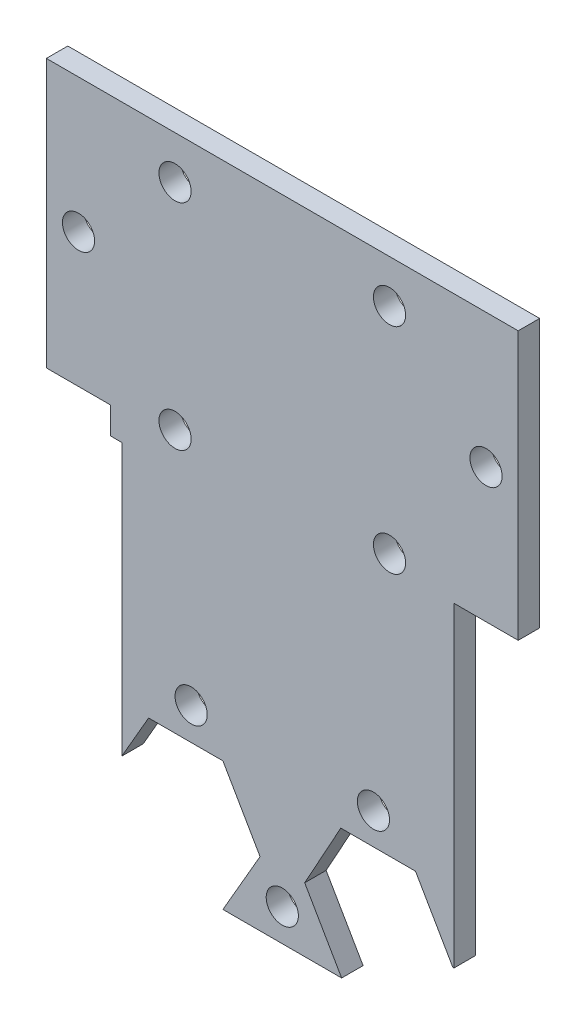
SolidWorks part; units mm, degrees
ref_plane "Front Plane" through (0, 0, 0) normal (0, 0, 1) x (1, 0, 0)
ref_plane "Top Plane" through (0, 0, 0) normal (0, 1, 0) x (1, 0, 0)
ref_plane "Right Plane" through (0, 0, 0) normal (1, 0, 0) x (0, 0, -1)
sketch "Sketch1" plane through (0, 0, 0) normal (0, 0, 1) x (1, 0, 0)
  line L0 (-15, -46.5) -> (15, -46.5) construction
  line L1 (-16, 14) -> (16, 14)
  line L2 (-16, 14) -> (-16, -13.5)
  line L3 (-16, -13.5) -> (16, -13.5)
  line L4 (16, 14) -> (16, -13.5)
  line L5 (-16, -13.5) -> (16, -13.5)
  line L6 (-16, -13.5) -> (-16, -46.5)
  line L7 (-16, -46.5) -> (16, -46.5)
  line L8 (16, -13.5) -> (16, -46.5)
  line L10 (-16, -46.5) -> (-14.9693, -46.5)
  line L11 (-16, -46.5) -> (-16, -13.5)
  line L12 (-16, -13.5) -> (-14.9693, -13.5)
  line L13 (-14.9693, -46.5) -> (-14.9693, -13.5)
  line L14 (15, -46.5) -> (15, -28.5) construction
  line L15 (16, -46.5) -> (15, -46.5)
  line L16 (16, -46.5) -> (16, -13.5)
  line L17 (16, -13.5) -> (15, -13.5)
  line L18 (15, -46.5) -> (15, -13.5)
  line L19 (16, -13.5) -> (-16, -13.5) construction
  line L20 (16, -13) -> (16, -6.5) construction
  line L21 (-16, 13.5) -> (16, 13.5) construction
  line L22 (-16, 14) -> (16, 14) construction
  line L23 (-16, 14) -> (-16, 39)
  line L24 (-16, 39) -> (16, 39)
  line L25 (16, 14) -> (16, 39)
  line L26 (9.5, 20.5152) -> (0, 15.0303)
  line L27 (0, 15.0303) -> (-9.5, 20.5152)
  line L28 (-9.5, 20.5152) -> (-9.5, 31.4848)
  line L29 (-9.5, 31.4848) -> (0, 36.9697)
  line L30 (0, 36.9697) -> (9.5, 31.4848)
  line L31 (9.5, 31.4848) -> (9.5, 20.5152)
  line L32 (9.5, 31.4848) -> (-9.5, 20.5152) construction
  line L33 (-9.5, 31.4848) -> (9.5, 20.5152) construction
  line L34 (0, 15.0303) -> (0, 36.9697) construction
  line L35 (15.9091, -40.467) -> (12.5423, -46.5671)
  line L36 (12.5423, -46.5671) -> (5.5747, -46.5671)
  line L37 (5.5747, -46.5671) -> (2.0909, -40.533)
  line L38 (2.0909, -40.533) -> (5.4577, -34.4329)
  line L39 (5.4577, -34.4329) -> (12.4253, -34.4329)
  line L40 (12.4253, -34.4329) -> (15.9091, -40.467)
  line L41 (12.4253, -34.4329) -> (5.5747, -46.5671) construction
  line L42 (2.0909, -40.533) -> (15.9091, -40.467) construction
  line L43 (12.5423, -46.5671) -> (5.4577, -34.4329) construction
  line L44 (-2.0718, -40.5) -> (-5.5359, -46.5)
  line L45 (-5.5359, -46.5) -> (-12.4641, -46.5)
  line L46 (-12.4641, -46.5) -> (-15.9282, -40.5)
  line L47 (-15.9282, -40.5) -> (-12.4641, -34.5)
  line L48 (-12.4641, -34.5) -> (-5.5359, -34.5)
  line L49 (-5.5359, -34.5) -> (-2.0718, -40.5)
  line L50 (-5.5359, -34.5) -> (-12.4641, -46.5) construction
  line L51 (-15.9282, -40.5) -> (-2.0718, -40.5) construction
  line L52 (-5.5359, -46.5) -> (-12.4641, -34.5) construction
  circle A0 centre (8.5, -31.5) radius 1.5
  circle A1 centre (-8.5, -31.5) radius 1.5
  circle A2 centre (0, -43.5) radius 1.5
  circle A3 centre (-10, -10) radius 1.5
  circle A4 centre (10, -10) radius 1.5
  circle A5 centre (10, 10) radius 1.5
  circle A6 centre (-10, 10) radius 1.5
  circle A7 centre (0, 26) radius 6.1
  point P51 (0, 26)
  point P61 (9, -40.5)
  point P70 (-9, -40.5)
  dimension "D1" = 3
  dimension "D2" = 3
  dimension "D3" = 3
  dimension "D4" = 3
  dimension "D5" = 3
  dimension "D6" = 3
  dimension "D7" = 3
  dimension "D9" = 12.2
  dimension "D10" = 12.5
  dimension "D15" = 27.5
  dimension "D8" = 25
  dimension "D11" = 19
  dimension "D12" = 120
  dimension "D13" = 120
  dimension "D14" = 16
  dimension "D16" = 12
  dimension "D17" = 120
  dimension "D19" = 12
  dimension "D20" = 120
extrude "Boss-Extrude2" add sketch "Sketch1" along normal blind 2 contours L7 L18 L5 L13 A2 A1 A0 | L18 L7 L8 L3 | L4 L1 L2 L3 L5 A6 A5 A4 A3
sketch "Sketch5" plane through (0, 0, 2) normal (0, 0, 1) x (1, 0, 0)
  line L0 (17.8253, -40.465) -> (-17.3183, -40.5014)
  line L1 (-17.3183, -40.5014) -> (-17.1295, -46.5)
  line L2 (-17.1295, -46.5) -> (17.9162, -46.5)
  line L3 (17.9162, -46.5) -> (17.8253, -40.465)
  line L4 (-9.5079, -40.4933) -> (-9.5079, -46.5)
  line L5 (-9.5079, -46.5) -> (10.3669, -46.5)
  line L6 (10.3669, -46.5) -> (10.3669, -40.4727)
  line M1 (15, -46.5) -> (16, -46.5)
  line M17 (15.9091, -40.467) -> (15, -42.1142)
  line M18 (15, -42.1142) -> (15, -46.5)
  line M62 (16, -46.5) -> (16, 14)
sketch "Sketch10" plane through (0, 0, 0) normal (0, 0, -1) x (-1, 0, 0)
  line L0 (0, 14) -> (0, -46.5) construction
  line L1 (16, 14) -> (22, 14)
  line L2 (16, 14) -> (16, -11)
  line L3 (16, -11) -> (22, -11)
  line L4 (22, 14) -> (22, -11)
  line L5 (16, 14) -> (22, -11) construction
  line L6 (16, -11) -> (22, 14) construction
  line L7 (16, 14) -> (16, -13.5) construction
  line L8 (5.5359, -46.5) -> (-5.5359, -46.5) construction
  line L9 (-16, -11) -> (-22, 14) construction
  line L10 (-16, 14) -> (-22, -11) construction
  line L11 (-22, 14) -> (-22, -11)
  line L12 (-16, -11) -> (-22, -11)
  line L13 (-16, 14) -> (-16, -11)
  line L14 (-16, 14) -> (-22, 14)
  line L15 (16, 14) -> (-16, 14) construction
  circle A0 centre (19, 1.5) radius 1.5
  circle A1 centre (-19, 1.5) radius 1.5
  point P4 (19, 1.5)
  point P20 (0, 0)
  point P21 (0, 0)
  dimension "D1" = 3
  dimension "D2" = 25
  dimension "D3" = 6
extrude "Boss-Extrude8" add sketch "Sketch10" against normal up to surface (2 mm away) up to face at (0.9337, -30.9011, 2)
extrude "Cut-Extrude1" cut sketch "Sketch5" against normal blind 10 contours L6 L2 L0 M18 M17 | L0 M62 M17 M18 M1 | L2 L3 L0 M62
